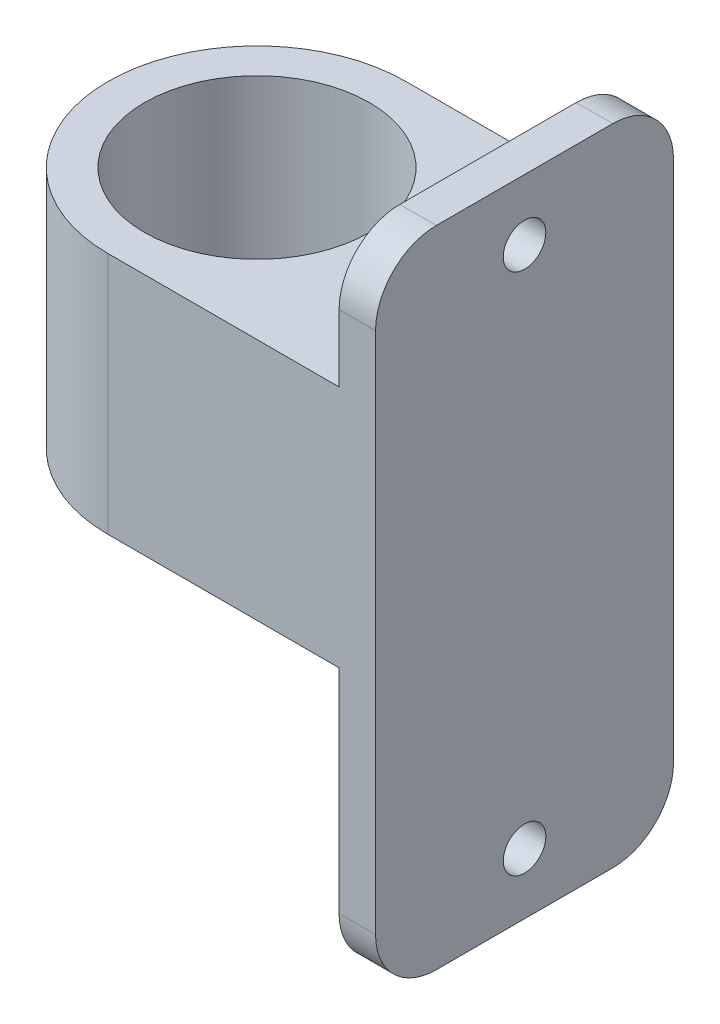
SolidWorks part; units mm, degrees
ref_plane "Front Plane" through (0, 0, 0) normal (0, 0, 1) x (1, 0, 0)
ref_plane "Top Plane" through (0, 0, 0) normal (0, 1, 0) x (1, 0, 0)
ref_plane "Right Plane" through (0, 0, 0) normal (1, 0, 0) x (0, 0, -1)
sketch "Sketch1" plane through (0, 0, 0) normal (0, 1, 0) x (1, 0, 0)
  line L0 (0, 9.25) -> (0, 12.25)
  line L1 (0, -12.25) -> (22, -12.25)
  line L2 (0, -12.25) -> (0, -9.25)
  line L3 (0, 12.25) -> (22, 12.25)
  line L4 (22, -12.25) -> (22, 12.25)
  circle A0 centre (0, 0) radius 9.25
  arc A1 (0, 12.25) -> (0, -12.25) centre (0, 0) ccw
  dimension "D1" = 18.5
  dimension "D2" = 3
  dimension "D3" = 22
extrude "Boss-Extrude1" add sketch "Sketch1" along normal blind 20 contours A0 L2 L1 L4 L3 L0 | L0 A1 L2 A0
sketch "Sketch2" plane through (22, 0, 0) normal (1, 0, 0) x (0, 0, -1)
  line L0 (-12.25, 10) -> (12.25, 10) construction
  line L1 (-12.25, 20) -> (12.25, 20)
  line L2 (-12.25, 20) -> (-12.25, 36.5)
  line L3 (-12.25, 36.5) -> (12.25, 36.5)
  line L4 (12.25, 20) -> (12.25, 36.5)
  line L5 (-12.25, 20) -> (-12.25, 0) construction
  line L6 (12.25, 20) -> (12.25, 0) construction
  line L7 (12.25, 0) -> (12.25, -16.5)
  line L8 (-12.25, -16.5) -> (12.25, -16.5)
  line L9 (-12.25, 0) -> (-12.25, -16.5)
  line L10 (-12.25, 0) -> (12.25, 0)
  circle A0 centre (0, 31.5) radius 1.75
  circle A1 centre (0, -11.5) radius 1.75
  point P10 (0, 36.5)
  dimension "D1" = 3.5
  dimension "D2" = 43
  dimension "D3" = 5
extrude "Boss-Extrude2" add sketch "Sketch2" against normal blind 3
fillet "Fillet1" radius 5 4 edges at (20.5, -16.5, -12.25) (20.5, -16.5, 12.25) (20.5, 36.5, 12.25) (20.5, 36.5, -12.25)
sketch "Sketch3" plane through (0, 0, 0) normal (0, -1, 0) x (1, 0, 0)
  line L3 (0, -12.25) -> (19, -12.25)
  line L4 (19, -12.25) -> (19, 12.25)
  line L5 (19, 12.25) -> (0, 12.25)
  line L6 (0, -12.25) -> (19, -12.25)
  line L7 (19, -12.25) -> (19, 12.25)
  line L8 (19, 12.25) -> (0, 12.25)
  circle A0 centre (0, 0) radius 9.25
  arc A1 (0, 12.25) -> (0, -12.25) centre (0, 0) ccw
  arc A2 (0, 12.25) -> (0, -12.25) centre (0, 0) ccw
  dimension "D1" = 0
sketch "Sketch4" plane through (0, 20, 0) normal (0, 1, 0) x (1, 0, 0)
  line L3 (0, -12.25) -> (19, -12.25)
  line L4 (19, -12.25) -> (19, 12.25)
  line L5 (19, 12.25) -> (0, 12.25)
  line L6 (0, -12.25) -> (19, -12.25)
  line L7 (19, -12.25) -> (19, 12.25)
  line L8 (19, 12.25) -> (0, 12.25)
  arc A1 (0, 12.25) -> (0, -12.25) centre (0, 0) ccw
  arc A2 (0, 12.25) -> (0, -12.25) centre (0, 0) ccw
  circle A3 centre (0, 0) radius 9.25
  dimension "D1" = 0
extrude "Boss-Extrude4" add sketch "Sketch4" along normal blind 6
extrude "Cut-Extrude1" cut sketch "Sketch3" against normal blind 6
